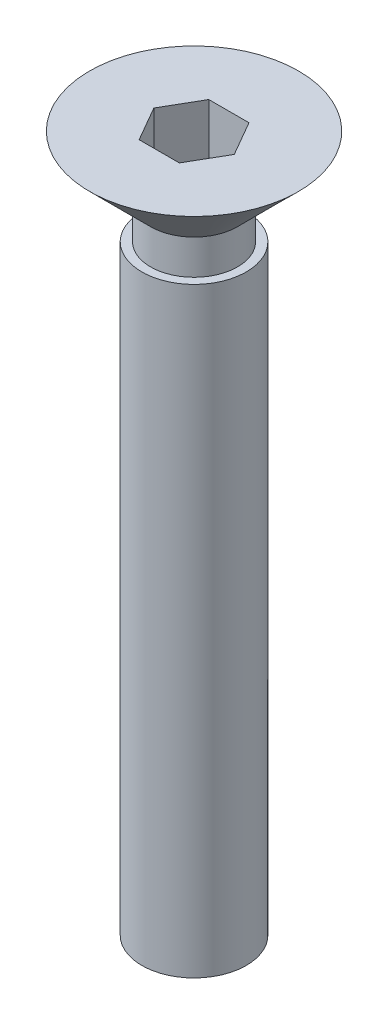
SolidWorks part; units mm, degrees
material "AISI 304"
ref_plane "前视基准面" through (0, 0, 0) normal (0, 0, 1) x (1, 0, 0)
ref_plane "上视基准面" through (0, 0, 0) normal (0, 1, 0) x (1, 0, 0)
ref_plane "右视基准面" through (0, 0, 0) normal (1, 0, 0) x (0, 0, -1)
sketch "草图1" plane through (0, 0, 0) normal (0, 0, 1) x (1, 0, 0)
  line L0 (0, 0) -> (0, 20) construction
  line L1 (0, 20) -> (-3, 20)
  line L2 (-3, 20) -> (-1.25, 18.25)
  line L3 (-1.25, 18.25) -> (-1.25, 17.25)
  line L4 (-1.25, 17.25) -> (-1.5, 17.25)
  line L5 (-1.5, 17.25) -> (-1.5, 0)
  line L6 (-1.5, 0) -> (0, 0)
  line L7 (0, 0) -> (0, 20)
  dimension "D1" = 6
  dimension "D2" = 45
  dimension "D3" = 3
  dimension "D4" = 20
  dimension "D5" = 1
  dimension "D6" = 2.5
revolve "旋转1" add sketch "草图1" angle 360 about L0
cosmetic thread "装饰螺纹线1" parameters "D2"=2.439
sketch "草图2" plane through (0, 20, 0) normal (0, 1, 0) x (1, 0, 0)
  line L1 (0.5774, 1) -> (-0.5774, 1)
  line L2 (-0.5774, 1) -> (-1.1547, 0)
  line L3 (-1.1547, 0) -> (-0.5774, -1)
  line L4 (-0.5774, -1) -> (0.5774, -1)
  line L5 (0.5774, -1) -> (1.1547, 0)
  line L6 (1.1547, 0) -> (0.5774, 1)
  circle A0 centre (0, 0) radius 1 construction
  dimension "D1" = 2
extrude "切除-拉伸1" cut sketch "草图2" against normal blind 2
